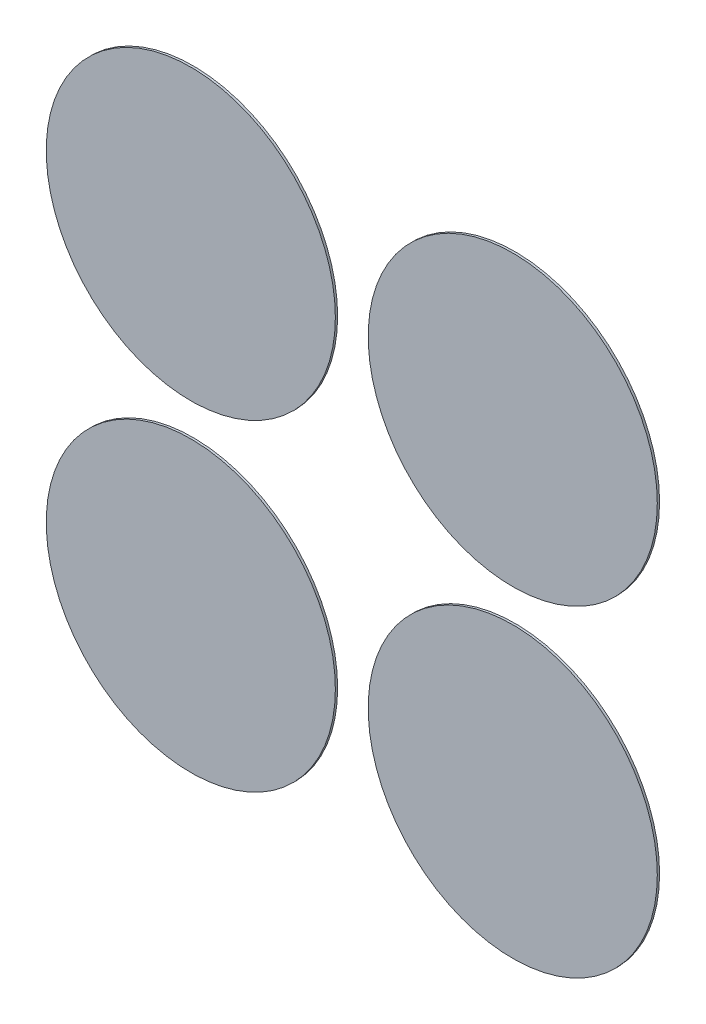
SolidWorks part; units mm, degrees
ref_plane "Front Plane" through (0, 0, 0) normal (0, 0, 1) x (1, 0, 0)
ref_plane "Top Plane" through (0, 0, 0) normal (0, 1, 0) x (1, 0, 0)
ref_plane "Right Plane" through (0, 0, 0) normal (1, 0, 0) x (0, 0, -1)
sketch "Sketch1" plane through (0, 0, 0) normal (0, 0, 1) x (1, 0, 0)
  line L0 (-133.0895, -90.0761) -> (-153.0895, -90.0761) construction
  line L1 (-143.0895, -80.0761) -> (-143.0895, -100.0761) construction
  line L2 (-143.0895, -90.0761) -> (-136.0184, -83.0051) construction
  line L3 (-143.0895, -90.0761) -> (-136.0184, -97.1472) construction
  line L4 (-143.0895, -90.0761) -> (-150.1605, -97.1472) construction
  line L5 (-143.0895, -90.0761) -> (-150.1605, -83.0051)
  circle A0 centre (-143.0895, -90.0761) radius 10 construction
  circle A1 centre (-136.0184, -83.0051) radius 6.35
  circle A2 centre (-136.0184, -97.1472) radius 6.35
  circle A3 centre (-150.1605, -97.1472) radius 6.35
  circle A4 centre (-150.1605, -83.0051) radius 6.35
extrude "Boss-Extrude2" add sketch "Sketch1" along normal blind 0.1 contours A1 | A2 | A3 | A4
